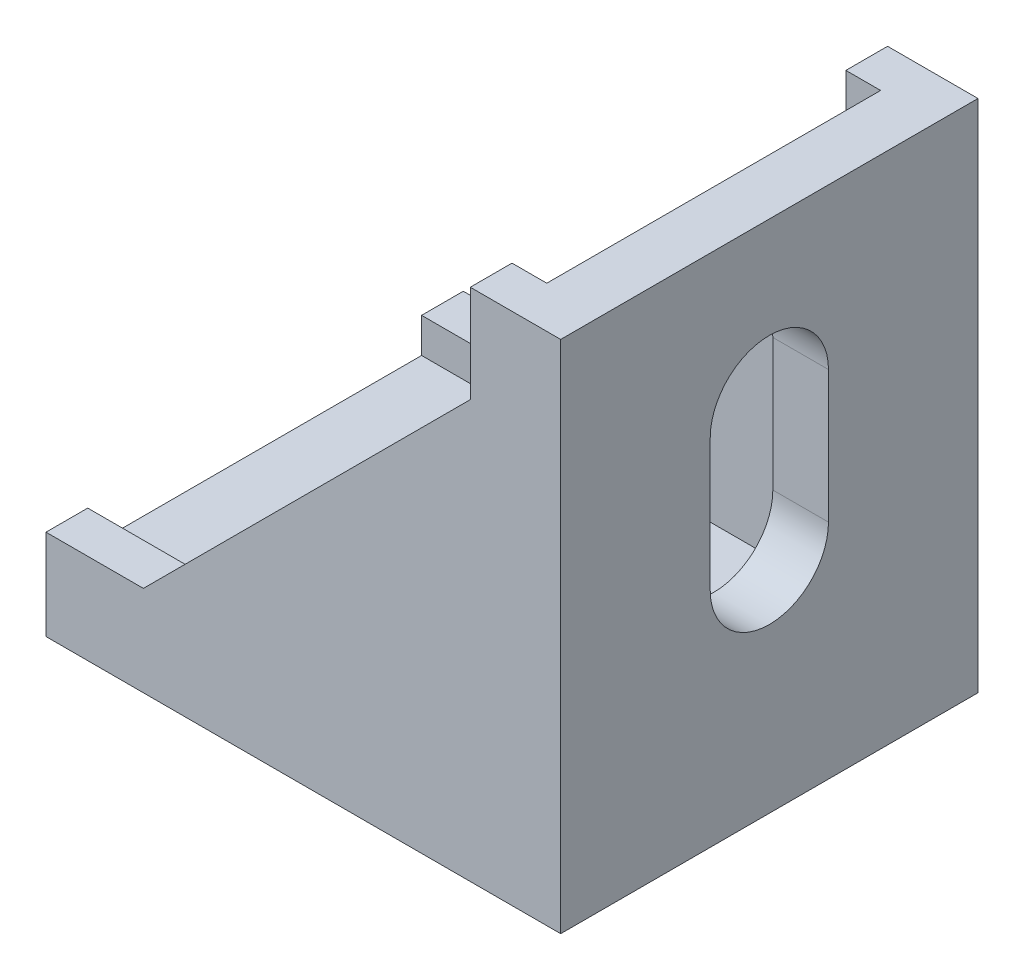
SolidWorks part; units mm, degrees
ref_plane "前视基准面" through (0, 0, 0) normal (0, 0, 1) x (1, 0, 0)
ref_plane "上视基准面" through (0, 0, 0) normal (0, 1, 0) x (1, 0, 0)
ref_plane "右视基准面" through (0, 0, 0) normal (1, 0, 0) x (0, 0, -1)
sketch "草图1" plane through (0, 0, 0) normal (0, 0, 1) x (1, 0, 0)
  line L0 (16.3393, 24.2098) -> (9.8393, 24.2098)
  line L3 (-20.6607, -12.7902) -> (16.3393, -12.7902)
  line L4 (16.3393, 24.2098) -> (16.3393, -12.7902)
  line L5 (9.8393, 24.2098) -> (9.8393, 17.2098)
  line L6 (32.676, -29.1269) -> (-33.6538, 37.2029) construction
  line L7 (-20.6607, -6.2902) -> (-13.6607, -6.2902)
  line L8 (-20.6607, -12.7902) -> (-20.6607, -6.2902)
  line L9 (-13.6607, -6.2902) -> (9.8393, 17.2098)
  dimension "D1" = 37
  dimension "D2" = 6.5
  dimension "D3" = 7
extrude "凸台-拉伸1" add sketch "草图1" along normal blind 30
sketch "草图3" plane through (-20.6607, 0, 0) normal (-1, 0, 0) x (0, 0, 1)
  line L0 (30, -6.2902) -> (30, -12.7902) construction
  line L1 (3, 26.44) -> (27, 26.44)
  line L2 (3, 26.44) -> (3, -8.7902)
  line L3 (3, -8.7902) -> (27, -8.7902)
  line L4 (27, 26.44) -> (27, -8.7902)
  line L5 (15, 37.5994) -> (15, -22.3839) construction
  line L6 (0, -6.2902) -> (0, -12.7902) construction
  line L7 (30, -12.7902) -> (0, -12.7902) construction
  dimension "D1" = 3
  dimension "D2" = 4
extrude "切除-拉伸1" cut sketch "草图3" against normal blind 33
sketch "草图4" plane through (0, -8.7902, 0) normal (0, 1, 0) x (1, 0, 0)
  line L0 (-36.9212, -15) -> (24.8326, -15) construction
  line L1 (9.8393, 0) -> (-13.6607, 0) construction
  line L2 (9.8393, -30) -> (-13.6607, -30) construction
  line L4 (16.3393, -30) -> (16.3393, 0) construction
  line L5 (-9.1607, -10.75) -> (0.3393, -10.75)
  line L6 (0.3393, -19.25) -> (-9.1607, -19.25)
  arc A0 (0.3393, -19.25) -> (0.3393, -10.75) centre (0.3393, -15) ccw
  arc A1 (-9.1607, -10.75) -> (-9.1607, -19.25) centre (-9.1607, -15) ccw
  dimension "D1" = 8.5
  dimension "D2" = 16
  dimension "D3" = 8.5
  dimension "D4" = 9.5
extrude "切除-拉伸2" cut sketch "草图4" against normal through all contours L5 A0 L6 A1
ref_plane "基准面1" through (1.7746, 1.7746, 0) normal (0.7071, 0.7071, 0) x (0.7071, -0.7071, 0)
mirror "镜向1" about plane through (1.7746, 1.7746, 0) normal (0.7071, 0.7071, 0) of "切除-拉伸2"
